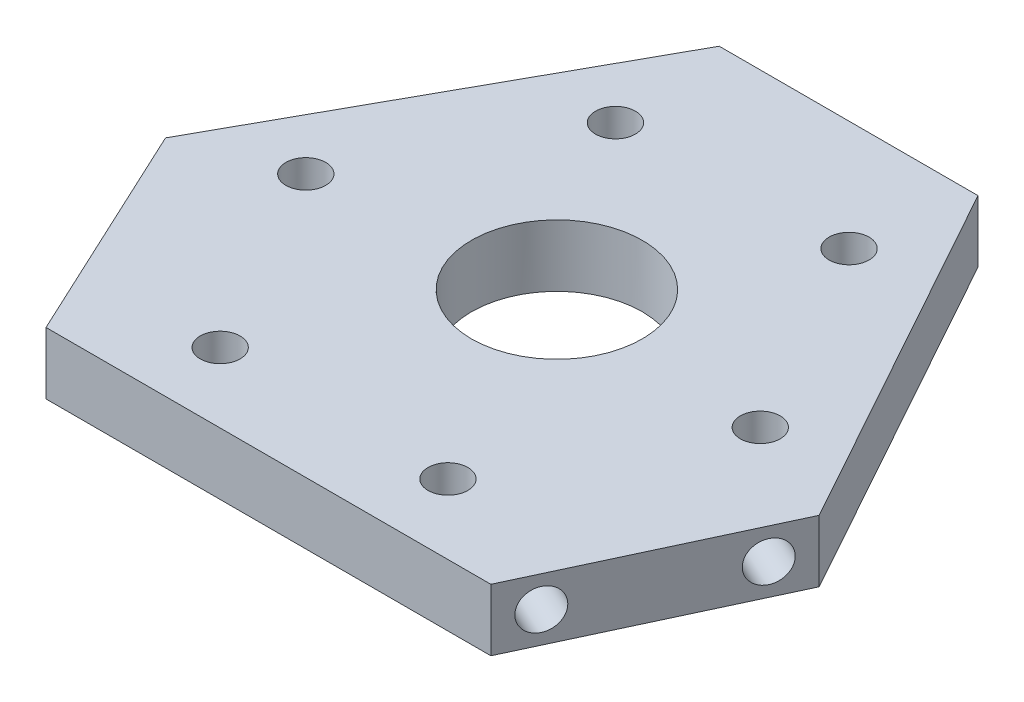
SolidWorks part; units mm, degrees
ref_plane "Front Plane" through (0, 0, 0) normal (0, 0, 1) x (1, 0, 0)
ref_plane "Top Plane" through (0, 0, 0) normal (0, 1, 0) x (1, 0, 0)
ref_plane "Right Plane" through (0, 0, 0) normal (1, 0, 0) x (0, 0, -1)
sketch "Sketch1" plane through (0, 0, 0) normal (0, 1, 0) x (1, 0, 0)
  line L0 (1.9657, 0) -> (57.1114, 0)
  line L1 (57.1114, 0) -> (70.0556, 27.7589)
  line L2 (1.9657, 0) -> (-10.9785, 27.7589)
  line L3 (-10.9785, 27.7589) -> (13.4997, 71.9187)
  line L4 (13.4997, 71.9187) -> (45.5774, 71.9187)
  line L5 (45.5774, 71.9187) -> (70.0556, 27.7589)
  dimension "D1" = 61
  dimension "D2" = 61
  dimension "D3" = 65
  dimension "D4" = 65
  dimension "D5" = 32.0777
  dimension "D6" = 55.1457
extrude "Boss-Extrude1" add sketch "Sketch1" along normal blind 6.5
scale "Scale1" scale about centroid uniform scaling yes scale factor 0.85
ref_plane "Plane1" through (0, 0, -35.5025) normal (0, 0, -1) x (-1, 0, 0)
sketch "Sketch2" plane through (0, 6.0125, 0) normal (0, 1, 0) x (1, 0, 0)
  circle A0 centre (29.561, 35.3073) radius 9
  dimension "D1" = 34.417
extrude "Cut-Extrude1" cut sketch "Sketch2" against normal blind 10
sketch "Sketch7" plane through (6.9029, 0, -3.2189) normal (-0.9063, 0, 0.4226) x (0.4226, 0, 0.9063)
  line L0 (-27.9301, 6.0125) -> (-27.9301, 0.4875) construction
  line L1 (-27.9301, 0.4875) -> (-1.8958, 0.4875) construction
  line L2 (-1.8958, 6.0125) -> (-1.8958, 0.4875) construction
  circle A0 centre (-23.9301, 3.2525) radius 2.1
  circle A1 centre (-5.8958, 3.2525) radius 2.1
  dimension "D1" = 4
  dimension "D2" = 2.765
  dimension "D3" = 2.765
  dimension "D4" = 4
extrude "Cut-Extrude7" cut sketch "Sketch7" against normal blind 6
sketch "Sketch8" plane through (0, 0, -66.068) normal (0, 0, -1) x (-1, 0, 0)
  line L0 (-43.1716, 6.0125) -> (-43.1716, 0.4875) construction
  line L1 (-15.9055, 6.0125) -> (-15.9055, 0.4875) construction
  line L2 (-43.1716, 0.4875) -> (-15.9055, 0.4875) construction
  circle A0 centre (-39.1716, 3.2525) radius 2.1
  circle A1 centre (-19.9055, 3.2525) radius 2.1
  dimension "D1" = 4
  dimension "D2" = 4
  dimension "D3" = 2.765
  dimension "D4" = 2.765
extrude "Cut-Extrude8" cut sketch "Sketch8" against normal blind 6
sketch "Sketch9" plane through (41.6227, 0, 19.409) normal (0.9063, 0, 0.4226) x (0.4226, 0, -0.9063)
  line L0 (26.8629, 6.0125) -> (26.8629, 0.4875) construction
  line L1 (52.8972, 6.0125) -> (52.8972, 0.4875) construction
  line L2 (26.8629, 0.4875) -> (52.8972, 0.4875) construction
  circle A0 centre (30.8629, 3.2525) radius 2.1
  circle A1 centre (48.8972, 3.2525) radius 2.1
  dimension "D1" = 4
  dimension "D2" = 4
  dimension "D3" = 2.765
  dimension "D4" = 2.765
extrude "Cut-Extrude9" cut sketch "Sketch9" against normal blind 6
sketch "Sketch10" plane through (0, 0.4875, 0) normal (0, -1, 0) x (1, 0, 0)
  circle A0 centre (41.2115, -54.4435) radius 2.1
  circle A1 centre (52.8469, -33.4526) radius 2.1
  circle A2 centre (17.4132, -53.6272) radius 2.1
  circle A3 centre (5.7777, -32.6364) radius 2.1
  circle A4 centre (17.1016, -12.2871) radius 2.1
  circle A5 centre (41.1016, -12.2871) radius 2.1
extrude "Cut-Extrude10" cut sketch "Sketch10" against normal blind 10
sketch "Sketch12" plane through (0, 6.0125, 0) normal (0, 1, 0) x (1, 0, 0)
  line L12 (-4.9009, 28.5322) -> (6.1016, 4.9371)
  line L13 (6.1016, 4.9371) -> (52.9755, 4.9371)
  line L14 (52.9755, 4.9371) -> (63.978, 28.5322)
  line L15 (63.978, 28.5322) -> (43.1716, 66.068)
  line L16 (43.1716, 66.068) -> (15.9055, 66.068)
  line L17 (15.9055, 66.068) -> (-4.9009, 28.5322)
  line L18 (-4.9009, 28.5322) -> (6.1016, 4.9371)
  line L19 (6.1016, 4.9371) -> (52.9755, 4.9371)
  line L20 (52.9755, 4.9371) -> (63.978, 28.5322)
  line L21 (63.978, 28.5322) -> (43.1716, 66.068)
  line L22 (43.1716, 66.068) -> (15.9055, 66.068)
  line L23 (15.9055, 66.068) -> (-4.9009, 28.5322)
  circle A0 centre (17.1016, 12.2871) radius 2.1 construction
  circle A1 centre (41.2115, 54.4435) radius 2.1 construction
  circle A2 centre (29.561, 35.3073) radius 9 construction
  circle A3 centre (5.7777, 32.6364) radius 2.1 construction
  circle A4 centre (41.1016, 12.2871) radius 2.1 construction
  circle A5 centre (52.8469, 33.4526) radius 2.1 construction
  circle A6 centre (17.4132, 53.6272) radius 2.1 construction
  circle A7 centre (17.1016, 12.2871) radius 2.1
  circle A8 centre (41.2115, 54.4435) radius 2.1
  circle A9 centre (29.561, 35.3073) radius 9
  circle A10 centre (5.7777, 32.6364) radius 2.1
  circle A11 centre (41.1016, 12.2871) radius 2.1
  circle A12 centre (52.8469, 33.4526) radius 2.1
  circle A13 centre (17.4132, 53.6272) radius 2.1
  dimension "D1" = 0
extrude "Boss-Extrude2" add sketch "Sketch12" along normal blind 0.5
sketch "Sketch13" plane through (0, 0.4875, 0) normal (0, -1, 0) x (1, 0, 0)
  line L6 (6.1016, -4.9371) -> (-4.9009, -28.5322)
  line L7 (-4.9009, -28.5322) -> (15.9055, -66.068)
  line L8 (15.9055, -66.068) -> (43.1716, -66.068)
  line L9 (43.1716, -66.068) -> (63.978, -28.5322)
  line L10 (63.978, -28.5322) -> (52.9755, -4.9371)
  line L11 (52.9755, -4.9371) -> (6.1016, -4.9371)
  line L12 (6.1016, -4.9371) -> (-4.9009, -28.5322)
  line L13 (-4.9009, -28.5322) -> (15.9055, -66.068)
  line L14 (15.9055, -66.068) -> (43.1716, -66.068)
  line L15 (43.1716, -66.068) -> (63.978, -28.5322)
  line L16 (63.978, -28.5322) -> (52.9755, -4.9371)
  line L17 (52.9755, -4.9371) -> (6.1016, -4.9371)
  circle A0 centre (41.1016, -12.2871) radius 2.1 construction
  circle A1 centre (17.1016, -12.2871) radius 2.1 construction
  circle A2 centre (5.7777, -32.6364) radius 2.1 construction
  circle A3 centre (41.2115, -54.4435) radius 2.1 construction
  circle A4 centre (29.561, -35.3073) radius 9 construction
  circle A5 centre (52.8469, -33.4526) radius 2.1 construction
  circle A6 centre (41.1016, -12.2871) radius 2.1
  circle A7 centre (17.1016, -12.2871) radius 2.1
  circle A8 centre (5.7777, -32.6364) radius 2.1
  circle A9 centre (41.2115, -54.4435) radius 2.1
  circle A10 centre (29.561, -35.3073) radius 9
  circle A11 centre (52.8469, -33.4526) radius 2.1
  circle A12 centre (17.4132, -53.6272) radius 2.1 construction
  circle A13 centre (17.4132, -53.6272) radius 2.1
  dimension "D1" = 0
extrude "Boss-Extrude3" add sketch "Sketch13" along normal blind 0.5
ref_plane "Plane2" through (6.1016, 0, 0) normal (-1, 0, 0) x (0, -1, 0)
ref_plane "Plane3" through (52.9755, 0, 0) normal (-1, 0, 0) x (0, -1, 0)
ref_plane "Plane4" through (29.5386, 0, 0) normal (-1, 0, 0) x (0, 0, 1)
